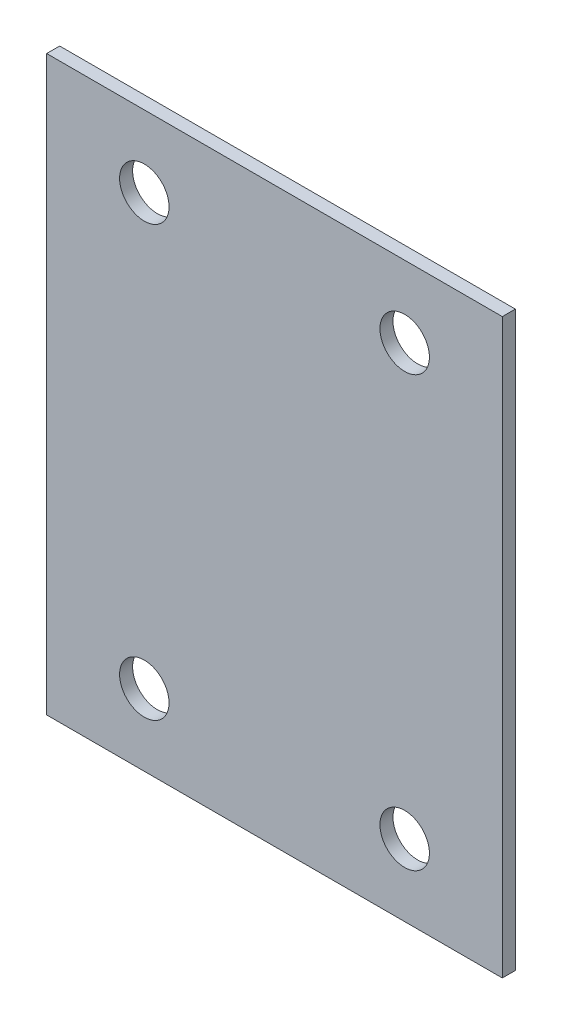
SolidWorks part; units mm, degrees
ref_plane "Спереди" through (0, 0, 0) normal (0, 0, 1) x (1, 0, 0)
ref_plane "Сверху" through (0, 0, 0) normal (0, 1, 0) x (1, 0, 0)
ref_plane "Справа" through (0, 0, 0) normal (1, 0, 0) x (0, 0, -1)
sketch "Эскиз1" plane through (0, 0, 0) normal (0, 0, 1) x (1, 0, 0)
  line L0 (175, -220) -> (175, 220)
  line L1 (175, 220) -> (-175, 220)
  line L2 (-175, 220) -> (-175, -220)
  line L3 (-175, -220) -> (175, -220)
  circle A4 centre (-100, 165) radius 19
  circle A5 centre (100, 165) radius 19
  circle A6 centre (100, -165) radius 19
  circle A7 centre (-100, -165) radius 19
extrude "Бобышка-Вытянуть1" add sketch "Эскиз1" along normal blind 10
